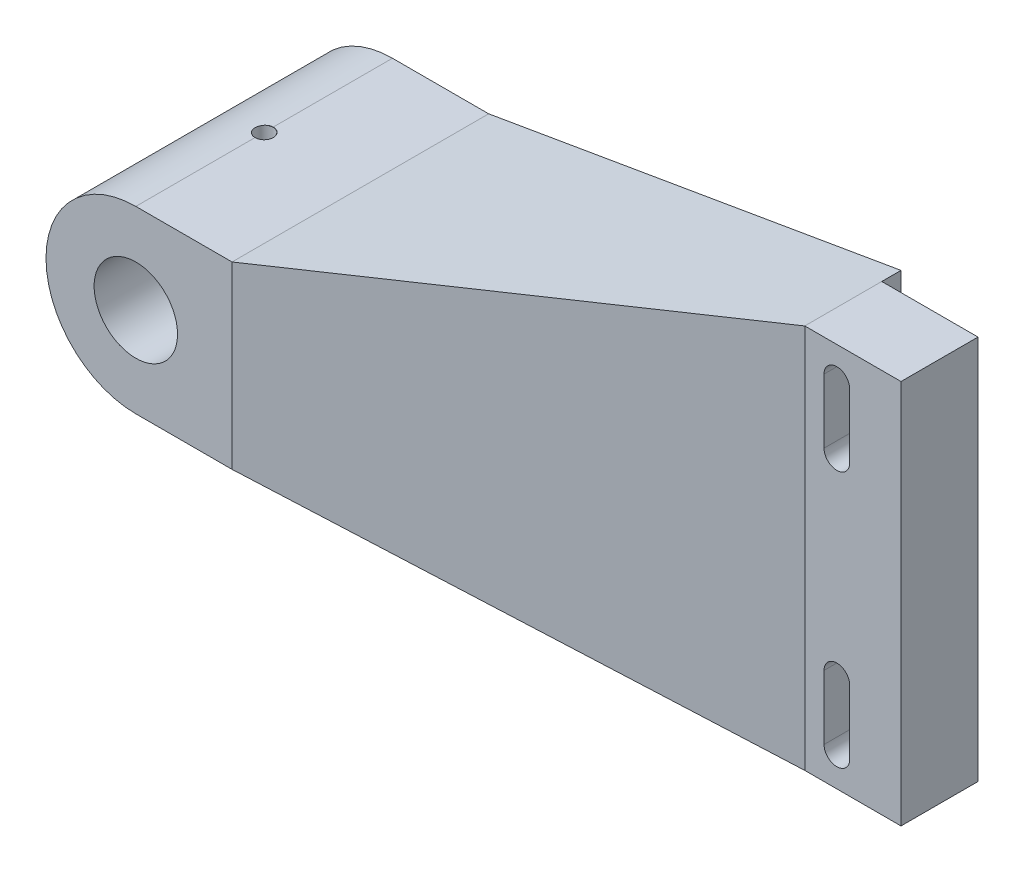
SolidWorks part; units mm, degrees
ref_plane "前基準面" through (0, 0, 0) normal (0, 0, 1) x (1, 0, 0)
ref_plane "上基準面" through (0, 0, 0) normal (0, 1, 0) x (1, 0, 0)
ref_plane "右基準面" through (0, 0, 0) normal (1, 0, 0) x (0, 0, -1)
sketch "草圖1" plane through (0, 0, 0) normal (0, 0, 1) x (1, 0, 0)
  line L1 (0, 14) -> (15, 14)
  line L2 (0, 14) -> (0, -14) construction
  line L3 (0, -14) -> (15, -14)
  line L4 (15, 14) -> (15, -14)
  circle A0 centre (0, 0) radius 6.5
  circle A1 centre (0, 0) radius 14
  dimension "D1" = 13
  dimension "D2" = 28
  dimension "D3" = 15
extrude "填料-伸長1" add sketch "草圖1" along normal blind 40 contours L2 A1 A0 | A1 L2 A0 | A1 L3 L4 L1
ref_plane "平面1" through (84.27, 0, 0) normal (1, 0, 0) x (0, 0, -1)
sketch "草圖2" plane through (84.27, 0, 0) normal (1, 0, 0) x (0, 0, -1)
  line L0 (-20, 30) -> (-40, 14) construction
  line L1 (-20, 30) -> (-5, 30)
  line L2 (-20, 30) -> (-20, -30)
  line L3 (-20, -30) -> (-5, -30)
  line L4 (-5, 30) -> (-5, -30)
  line L5 (-5, 30) -> (0, 14) construction
  line L6 (0, -14) -> (-5, -30) construction
  line L8 (0, -14) -> (0, 14)
  line L9 (0, 14) -> (-40, 14)
  line L10 (-40, 14) -> (-40, -14)
  line L11 (-40, -14) -> (0, -14)
  line L12 (0, -14) -> (0, 14) construction
  line L13 (0, 14) -> (-40, 14) construction
  line L14 (-40, 14) -> (-40, -14) construction
  line L15 (-40, -14) -> (0, -14) construction
  dimension "D2" = 60
  dimension "D3" = 15
  dimension "D4" = 10
  dimension "D1" = 0
loft "疊層拉伸1" add profiles "草圖2" section face at (15, 0, 20) section "草圖2"
sketch "草圖3" plane through (84.27, 0, 0) normal (1, 0, 0) x (0, 0, -1)
  line L0 (-5, 30) -> (-20, 30) construction
  line L1 (-20, 30) -> (-8, 30)
  line L2 (-20, 30) -> (-20, -30)
  line L3 (-20, -30) -> (-8, -30)
  line L4 (-8, 30) -> (-8, -30)
  line L5 (-20, -30) -> (-5, -30) construction
  line L6 (-5, -30) -> (-5, 30) construction
  line L8 (-20, 30) -> (-20, -30) construction
  dimension "D1" = 3
extrude "填料-伸長2" add sketch "草圖3" along normal blind 15
sketch "草圖4" plane through (0, 0, 20) normal (0, 0, 1) x (1, 0, 0)
  line L0 (89.27, 25) -> (89.27, 15) construction
  line L1 (91.27, 25) -> (91.27, 15)
  line L2 (87.27, 25) -> (87.27, 15)
  line L3 (89.27, -15) -> (89.27, -25) construction
  line L4 (91.27, -15) -> (91.27, -25)
  line L5 (87.27, -15) -> (87.27, -25)
  line L6 (84.27, 30) -> (89.27, 25) construction
  line L7 (89.27, -25) -> (84.27, -30) construction
  line L8 (84.27, 30) -> (84.27, -30) construction
  arc A0 (91.27, 25) -> (87.27, 25) centre (89.27, 25) ccw
  arc A1 (87.27, 15) -> (91.27, 15) centre (89.27, 15) ccw
  arc A2 (91.27, -15) -> (87.27, -15) centre (89.27, -15) ccw
  arc A3 (87.27, -25) -> (91.27, -25) centre (89.27, -25) ccw
  point P2 (89.27, 20)
  point P7 (89.27, -20)
  dimension "D1" = 5
  dimension "D2" = 4
  dimension "D3" = 10
  dimension "D4" = 40
extrude "除料-伸長1" cut sketch "草圖4" against normal through all
hole_wizard "Ø2.8 (2.8) 直徑孔1" positions "草圖5" profile "草圖6" hole size "Ø2.8" standard "ISO" end condition through all
sketch "草圖5" plane through (0, 14, 0) normal (0, 1, 0) x (1, 0, 0)
  line L0 (0, -40) -> (0, 0) construction
  point P0 (0, -20)
sketch "草圖6" plane through (0, 14, 20) normal (1, 0, 0) x (0, 0, 1)
  line L0 (0, 0) -> (0, 44.0001)
  line L1 (0, 44.0001) -> (1.4, 44.0001)
  line L2 (1.4, 44.0001) -> (1.4, 0.025)
  line L3 (1.4, 0.025) -> (1.425, 0)
  line L5 (1.425, 0) -> (0, 0)
  line L6 (-1.4, 0.025) -> (-1.425, 0) construction
  line L11 (0, -6.35) -> (0, 107.95) construction
  dimension "貫穿孔直徑" = 2.8
  dimension "貫穿孔深度" = 44.0001
  dimension "近端錐孔直徑" = 2.85
  dimension "近端錐孔角度" = 90
